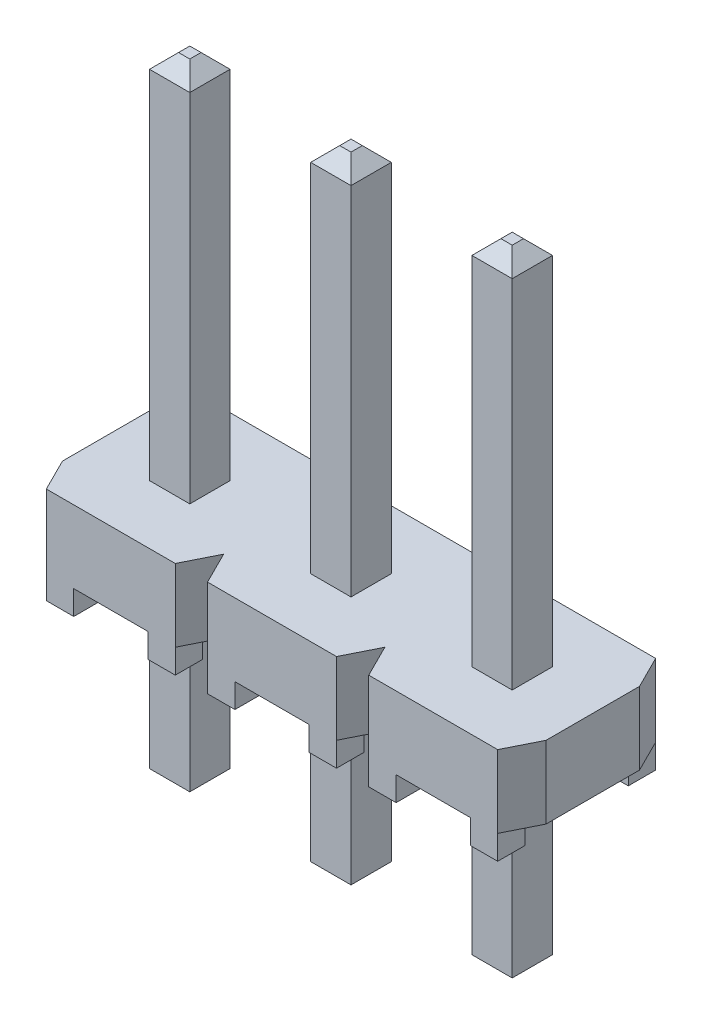
SolidWorks part; units mm, degrees
ref_plane "Front" through (0, 0, 0) normal (0, 0, 1) x (1, 0, 0)
ref_plane "Top" through (0, 0, 0) normal (0, 1, 0) x (1, 0, 0)
ref_plane "Side" through (0, 0, 0) normal (1, 0, 0) x (0, 0, -1)
sketch "Sketch1" plane through (0, 0, 0) normal (0, 1, 0) x (1, 0, 0)
  line L0 (3.81, -1.2446) -> (-3.81, 1.2446) construction
  line L1 (-3.81, 1.2446) -> (3.81, 1.2446)
  line L2 (-3.81, 1.2446) -> (-3.81, -1.2446)
  line L3 (-3.81, -1.2446) -> (3.81, -1.2446)
  line L4 (3.81, 1.2446) -> (3.81, -1.2446)
  dimension "D1" = 7.62
  dimension "D2" = 2.4892
extrude "Base-Extrude" add sketch "Sketch1" along normal mid plane 1.143
sketch "Sketch3" plane through (0, 0.5715, 0) normal (0, 1, 0) x (-1, 0, 0)
  line L0 (7.5339, 0) -> (10.4044, 0) construction
  line L1 (1.016, 1.2446) -> (1.524, 1.2446)
  line L2 (1.016, -1.2446) -> (1.524, -1.2446)
  line L3 (1.524, 1.2446) -> (1.27, 0.7366)
  line L4 (1.524, -1.2446) -> (1.27, -0.7366)
  line L5 (1.27, 0.7366) -> (1.016, 1.2446)
  line L6 (1.27, -0.7366) -> (1.016, -1.2446)
  line L7 (1.27, 1.2446) -> (1.27, 0.7366) construction
  line L8 (1.27, -1.2446) -> (1.27, -0.7366) construction
  line L9 (3.81, 1.2446) -> (-3.81, 1.2446) construction
  line L11 (2.54, -1.4521) -> (2.54, 2.3817) construction
  line L12 (3.81, -0.7366) -> (4.064, -1.2446)
  line L13 (3.81, 0.7366) -> (4.064, 1.2446)
  line L14 (3.556, -1.2446) -> (3.81, -0.7366)
  line L15 (3.556, 1.2446) -> (3.81, 0.7366)
  line L16 (4.064, -1.2446) -> (3.556, -1.2446)
  line L17 (4.064, 1.2446) -> (3.556, 1.2446)
  line L18 (3.81, -1.2446) -> (3.81, 1.2446) construction
  dimension "D1" = 0.508
  dimension "D2" = 0.508
  dimension "D3" = 1.27
  dimension "D4" = 1.27
extrude "Snap Grooves" cut sketch "Sketch3" against normal through all
sketch "Sketch4" plane through (0, -0.5715, 0) normal (0, -1, 0) x (1, 0, 0)
  line L0 (-2.54, 1.3819) -> (-2.54, -1.499) construction
  line L1 (-3.556, 1.2446) -> (-1.524, 1.2446) construction
  line L2 (-3.556, 1.2446) -> (-3.1242, 1.2446)
  line L3 (-3.556, 1.2446) -> (-3.556, 0.8128)
  line L4 (-3.556, 0.8128) -> (-3.1242, 0.8128)
  line L5 (-3.1242, 1.2446) -> (-3.1242, 0.8128)
  line L6 (-1.9558, 1.2446) -> (-1.9558, 0.8128)
  line L7 (-1.524, 0.8128) -> (-1.9558, 0.8128)
  line L8 (-1.524, 1.2446) -> (-1.524, 0.8128)
  line L9 (-1.524, 1.2446) -> (-1.9558, 1.2446)
  line L11 (-3.81, -0.7366) -> (-3.81, 0.7366) construction
  line L12 (-9.3213, 0) -> (-10.8923, 0) construction
  line L14 (-1.524, -1.2446) -> (-1.9558, -1.2446)
  line L15 (-1.524, -1.2446) -> (-1.524, -0.8128)
  line L16 (-1.524, -0.8128) -> (-1.9558, -0.8128)
  line L17 (-1.9558, -1.2446) -> (-1.9558, -0.8128)
  line L18 (-3.1242, -1.2446) -> (-3.1242, -0.8128)
  line L19 (-3.556, -0.8128) -> (-3.1242, -0.8128)
  line L20 (-3.556, -1.2446) -> (-3.556, -0.8128)
  line L21 (-3.556, -1.2446) -> (-3.1242, -1.2446)
  dimension "D1" = 0.4318
  dimension "D2" = 0.4318
  dimension "D3" = 1.27
extrude "Standoffs" add sketch "Sketch4" along normal blind 0.381
pattern_linear "Position Pattern" count 3 spacing 2.54 along (1, 0, 0) of "Snap Grooves", "Standoffs"
ref_plane "Position 1 Plane" through (-2.54, 0, 0) normal (-1, 0, 0) x (0, 0, 1)
sketch "Sketch5" plane through (-2.54, 0, 0) normal (-1, 0, 0) x (0, 0, 1)
  line L0 (0, 6.4135) -> (0, -3.5865) construction
  line L1 (-0.3175, 6.4135) -> (0.3175, 6.4135)
  line L2 (-0.3175, 6.4135) -> (-0.3175, -3.5865)
  line L3 (-0.3175, -3.5865) -> (0.3175, -3.5865)
  line L4 (0.3175, 6.4135) -> (0.3175, -3.5865)
  line L5 (1.2446, -0.5715) -> (1.2446, 0.5715) construction
  line L6 (-0.7366, 0.5715) -> (0.7366, 0.5715) construction
  dimension "D1" = 1.2446
  dimension "D2" = 0.635
  dimension "D3" = 5.842
  dimension "D4" = 10
extrude "Terminal -TH" add sketch "Sketch5" along normal mid plane 0.635
chamfer "T1 Tip1" distance 0.2286 angle 45 8 edges at (-2.2225, 6.4135, 0) (-2.54, 6.4135, -0.3175) (-2.8575, 6.4135, 0) (-2.54, 6.4135, 0.3175) (-2.54, -3.5865, -0.3175) (-2.8575, -3.5865, 0) (-2.54, -3.5865, 0.3175) (-2.2225, -3.5865, 0)
pattern_linear "Terminal Pattern" count 1 spacing 2.54 along (0, 0, 1) count 3 spacing 2.54 along (1, 0, 0) of "Terminal -TH", "T1 Tip1"
ref_plane "Initial -S Polarize Plane" through (5.08, 0, 0) normal (1, 0, 0) x (0, 0, -1)
ref_plane "-S Polarize Plane" through (2.54, 0, 0) normal (1, 0, 0) x (0, 0, -1)
ref_plane "Initial -D Polarize Plane" through (-5.08, 0, 0) normal (-1, 0, 0) x (0, 0, 1)
ref_plane "-D Polarize Plane" through (-3.81, 0, 0) normal (-1, 0, 0) x (0, 0, 1)
